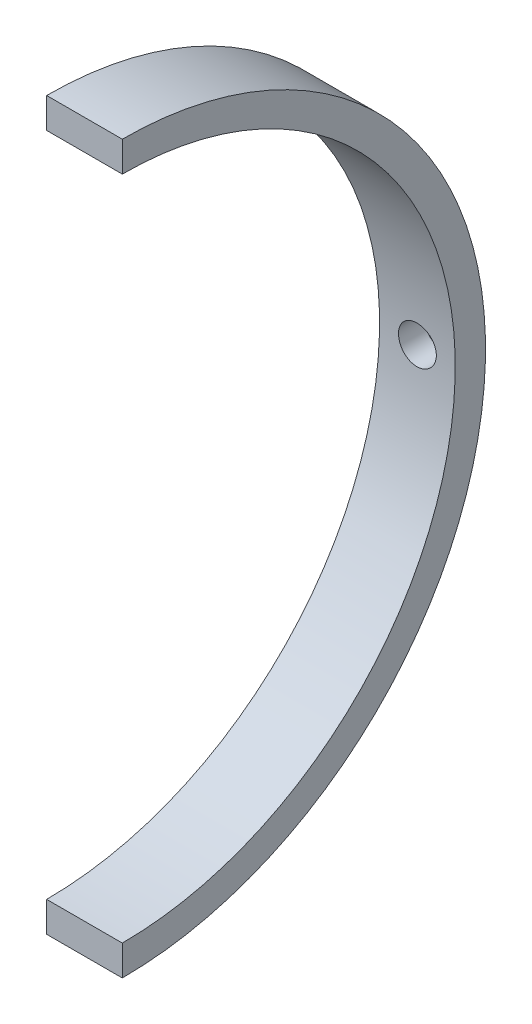
SolidWorks part; units mm, degrees
material "2018 slitina"
ref_plane "Přední rovina" through (0, 0, 0) normal (0, 0, 1) x (1, 0, 0)
ref_plane "Horní rovina" through (0, 0, 0) normal (0, 1, 0) x (1, 0, 0)
ref_plane "Pravá rovina" through (0, 0, 0) normal (1, 0, 0) x (0, 0, -1)
sketch "Skica1" plane through (0, 0, 0) normal (0, 0, 1) x (1, 0, 0)
  line L0 (-358.05, -21.9773) -> (-358.05, 22) construction
  line L1 (-353.05, 24) -> (-353.05, -23.9792) construction
  line L2 (-358.05, -21.9773) -> (-358.05, 22) construction
  line L3 (-353.05, 24) -> (-353.05, -23.9792) construction
  line L4 (-344.9045, 0) -> (-368.3346, 0) construction
  line L5 (-353.05, 24) -> (-358.05, 24)
  line L6 (-353.05, 24) -> (-353.05, 22)
  line L7 (-353.05, 22) -> (-358.05, 22)
  line L8 (-358.05, 24) -> (-358.05, 22)
revolve "Rotovat1" add sketch "Skica1" angle 180 about L4
ref_plane "Rovina1" through (0, 0, -24) normal (0, 0, -1) x (-1, 0, 0)
sketch "Skica2" plane through (0, 0, -24) normal (0, 0, -1) x (-1, 0, 0)
  line L0 (358.05, -24) -> (358.05, 24) construction
  line L1 (353.05, 24) -> (353.05, -24) construction
  line L2 (358.05, -24) -> (358.05, 24) construction
  line L3 (353.05, 24) -> (353.05, -24) construction
  line L4 (353.05, 24) -> (358.05, -24) construction
  point P4 (355.55, 0)
hole_wizard "M3 závit1" positions "3DSkica1" profile "Skica3" tap size "M3" standard "ISO"
sketch3d "3DSkica1"
  point P0 (-355.55, 0, -24)
sketch "Skica3" plane through (-355.55, 0, -24) normal (1, 0, 0) x (0, 1, 0)
  line L0 (0, 0) -> (0, 2)
  line L1 (0, 2) -> (1.25, 2)
  line L2 (1.25, 2) -> (1.25, 0.275)
  line L3 (1.25, 0.275) -> (1.525, 0)
  line L5 (1.525, 0) -> (0, 0)
  line L6 (-1.25, 0.275) -> (-1.525, 0) construction
  line L11 (0, -6.35) -> (0, 107.95) construction
  dimension "Průměr závitníku" = 2.5
  dimension "Hloubka závitníku" = 2
  dimension "Průměr blíz. kuž. zahloubení" = 3.05
  dimension "Úhel blíz. kuž. zahloubení" = 90
cosmetic thread "Závit díry1" parameters "D2"=3
